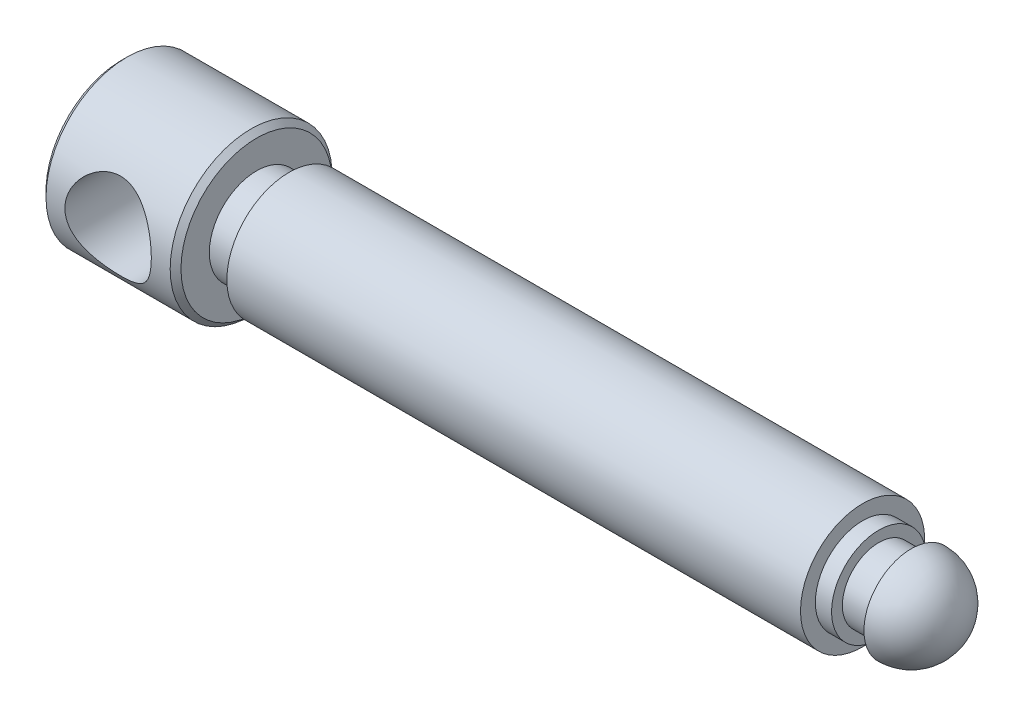
SolidWorks part; units mm, degrees
material "1.8901 (S460N)"
ref_plane "Front Plane" through (0, 0, 0) normal (0, 0, 1) x (1, 0, 0)
ref_plane "Top Plane" through (0, 0, 0) normal (0, 1, 0) x (1, 0, 0)
ref_plane "Right Plane" through (0, 0, 0) normal (1, 0, 0) x (0, 0, -1)
sketch "Sketch1" plane through (0, 0, 0) normal (0, 0, 1) x (1, 0, 0)
  line L0 (-145.2273, 0) -> (139.0071, 0) construction
  line L1 (221.4013, 0) -> (-221.4013, 0) construction
  line L2 (-263.5406, 0) -> (-263.5406, 30)
  line L3 (-263.5406, 30) -> (-213.5406, 30)
  line L4 (-213.5406, 30) -> (-213.5406, 17.5)
  line L5 (-213.5406, 17.5) -> (-201.5406, 17.5)
  line L6 (-201.5406, 17.5) -> (-201.5406, 23)
  line L7 (-201.5406, 23) -> (10.9594, 23)
  line L8 (10.9594, 23) -> (10.9594, 17.5)
  line L9 (10.9594, 17.5) -> (16.9594, 17.5)
  line L10 (16.9594, 17.5) -> (16.9594, 13.5)
  line L11 (16.9594, 13.5) -> (28.9594, 13.5)
  line L15 (-263.5406, 0) -> (46.4594, 0)
  line L16 (28.9594, 13.5) -> (28.9594, 17.5)
  line L17 (28.9594, 13.5) -> (28.9594, 0) construction
  arc A1 (28.9594, 17.5) -> (46.4594, 0) centre (28.9594, 0) cw
  point P22 (16.9594, 15.5)
  dimension "D10" = 17.5
  dimension "D5" = 10.9594
  dimension "D1" = 50
  dimension "D2" = 310
  dimension "D3" = 5.5
  dimension "D4" = 30
  dimension "D6" = 12
  dimension "D7" = 15.5
  dimension "D8" = 212.5
  dimension "D9" = 23
  dimension "D12" = 6
  dimension "D13" = 12
revolve "Revolve1" add sketch "Sketch1" angle 360 about L0
cosmetic thread "Cosmetic Thread1" parameters "D2"=40.066
chamfer "Chamfer1" distance 2 angle 45 2 edges at (-213.5406, 0, 30) (-263.5406, 0, 30)
ref_plane "Plane1" through (0, 0, 30) normal (0, 0, 1) x (1, 0, 0)
sketch "Sketch5" plane through (0, 0, 30) normal (0, 0, 1) x (1, 0, 0)
  line L0 (221.4013, 0) -> (-221.4013, 0) construction
  line L1 (-263.5406, 28) -> (-263.5406, -28) construction
  circle A0 centre (-238.5406, 0) radius 16
  dimension "D1" = 32
  dimension "D2" = 25
extrude "Cut-Extrude2" cut sketch "Sketch5" against normal through all
